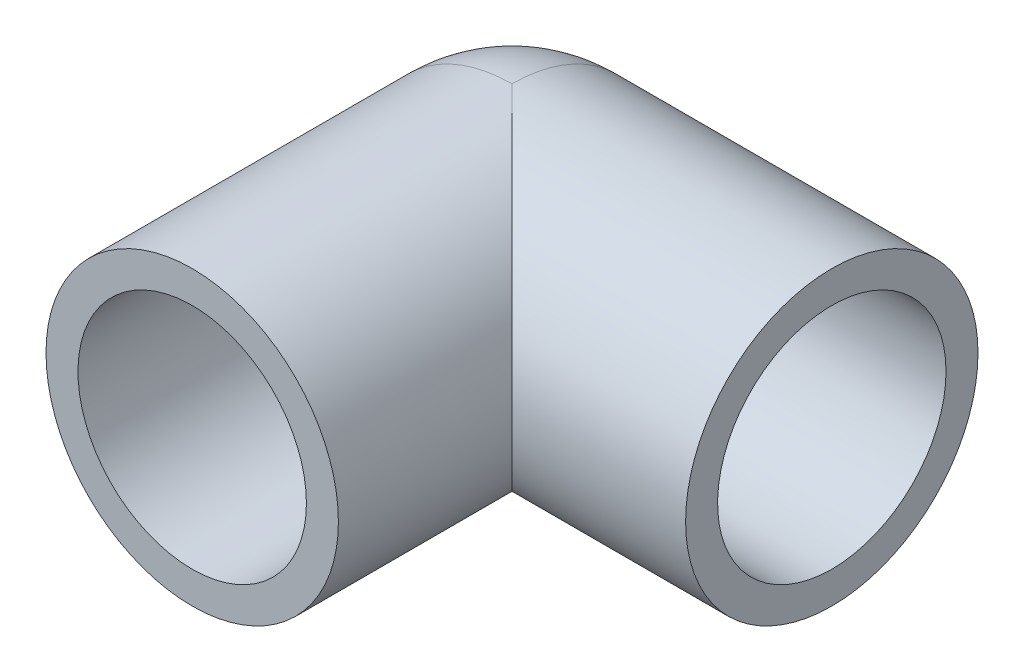
SolidWorks part; units mm, degrees
ref_plane "前视基准面" through (0, 0, 0) normal (0, 0, 1) x (1, 0, 0)
ref_plane "上视基准面" through (0, 0, 0) normal (0, 1, 0) x (1, 0, 0)
ref_plane "右视基准面" through (0, 0, 0) normal (1, 0, 0) x (0, 0, -1)
other "Configuration Table"
sketch "草图1" plane through (0, 0, 0) normal (0, 0, 1) x (1, 0, 0)
  circle A0 centre (0, 0) radius 12.5
  circle A1 centre (0, 0) radius 16
  dimension "D1" = 25
  dimension "D2" = 32
extrude "凸台-拉伸1" add sketch "草图1" along normal blind 35
sketch "草图2" plane through (0, 0, 0) normal (1, 0, 0) x (0, 0, -1)
  circle A0 centre (0, 0) radius 16
  circle A1 centre (0, 0) radius 12.5
  dimension "D1" = 32
  dimension "D2" = 25
extrude "凸台-拉伸2" add sketch "草图2" along normal blind 35
sketch "草图3" plane through (0, 0, 0) normal (0, 0, 1) x (1, 0, 0)
  line L0 (0, 16) -> (0, -16)
  arc A0 (0, 16) -> (0, -16) centre (0, 0) ccw
  circle A1 centre (0, 0) radius 16 construction
  point P5 (0, 16)
revolve "旋转1" add sketch "草图3" angle 90 about L0
